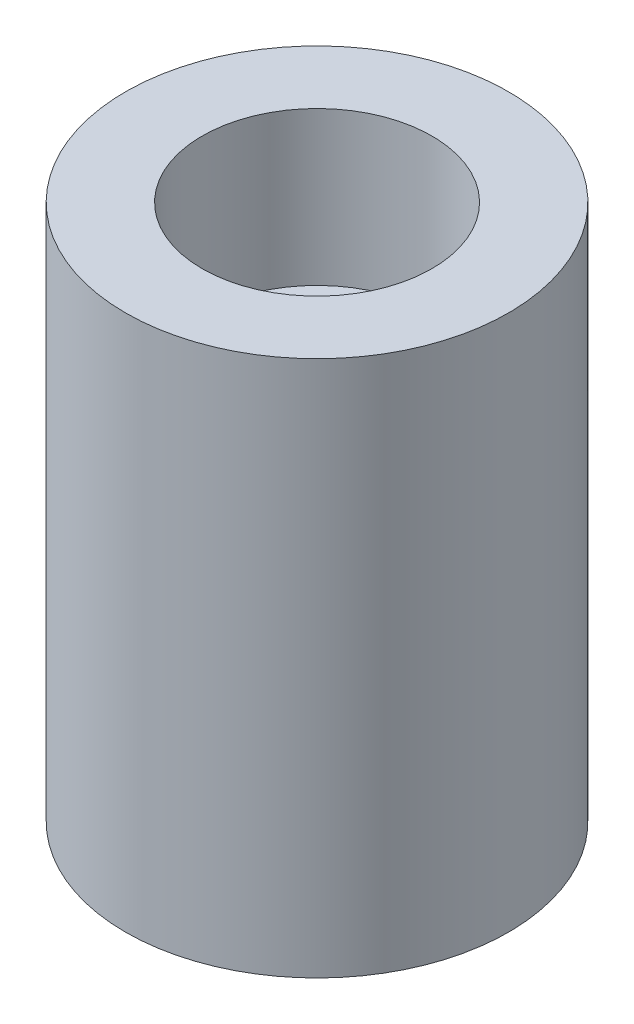
SolidWorks part; units mm, degrees
ref_plane "Front Plane" through (0, 0, 0) normal (0, 0, 1) x (1, 0, 0)
ref_plane "Top Plane" through (0, 0, 0) normal (0, 1, 0) x (1, 0, 0)
ref_plane "Right Plane" through (0, 0, 0) normal (1, 0, 0) x (0, 0, -1)
sketch "Sketch3" plane through (0, 0, 0) normal (0, 1, 0) x (1, 0, 0)
  circle A0 centre (0, 0) radius 50
  dimension "D1" = 100
extrude "Boss-Extrude3" add sketch "Sketch3" along normal blind 140
sketch "Sketch4" plane through (0, 140, 0) normal (0, 1, 0) x (1, 0, 0)
  circle A0 centre (0, 0) radius 30
  dimension "D1" = 60
extrude "Cut-Extrude1" cut sketch "Sketch4" against normal blind 40
sketch "Sketch5" plane through (0, 100, 0) normal (0, 1, 0) x (1, 0, 0)
  circle A0 centre (0, 0) radius 10
  dimension "D1" = 20
extrude "Cut-Extrude2" cut sketch "Sketch5" against normal blind 80
